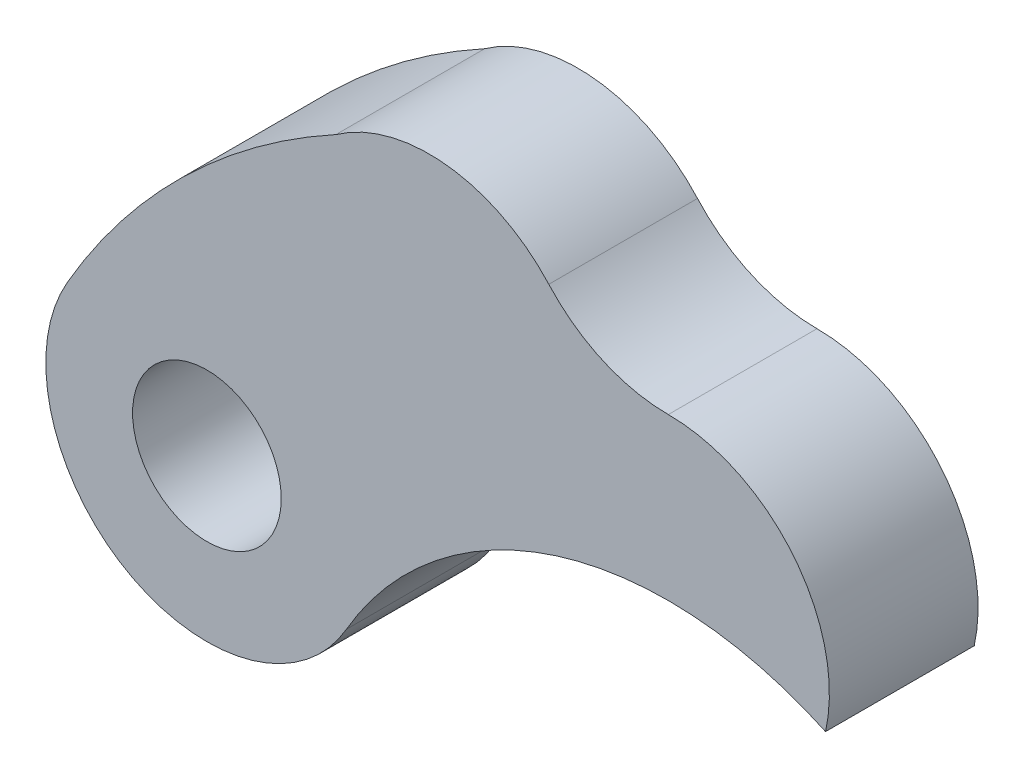
SolidWorks part; units mm, degrees
ref_plane "Plan de face" through (0, 0, 0) normal (0, 0, 1) x (1, 0, 0)
ref_plane "Plan de dessus" through (0, 0, 0) normal (0, 1, 0) x (1, 0, 0)
ref_plane "Plan de droite" through (0, 0, 0) normal (1, 0, 0) x (0, 0, -1)
sketch "Esquisse1" plane through (0, 0, 0) normal (0, 0, 1) x (1, 0, 0)
  line L2 (-9.3098, 5.375) -> (5.2544, 5.375) construction
  line L4 (-7.6848, 2.5604) -> (-9.3098, 5.375) construction
  arc A12 (-2.411, 11.8207) -> (0, 10.75) centre (0, 14) ccw
  arc A17 (-2.411, 11.8207) -> (-6.7074, 12.2887) centre (-4.8221, 9.6414) ccw
  arc A18 (-6.7074, 12.2887) -> (-12.1244, 7) centre (0, 0) ccw
  circle A33 centre (-9.3098, 5.375) radius 1.5
  arc A35 (-12.1244, 7) -> (-6.4952, 3.75) centre (-9.3098, 5.375) ccw
  arc A38 (3.1728, 6.7958) -> (0, 10.75) centre (0, 7.5) ccw
  arc A39 (0, 10.75) -> (-10.4906, 2.3471) centre (0, 0) ccw construction
  arc A40 (3.1728, 6.7958) -> (-6.4952, 3.75) centre (0, 0) ccw
  point P31 (0, 0)
  dimension "D2" = 6.5
  dimension "D3" = 6.5
  dimension "D8" = 14
  dimension "D9" = 3.25
  dimension "D15" = 10.78
extrude "Boss.-Extru.2" add sketch "Esquisse1" along normal blind 3
